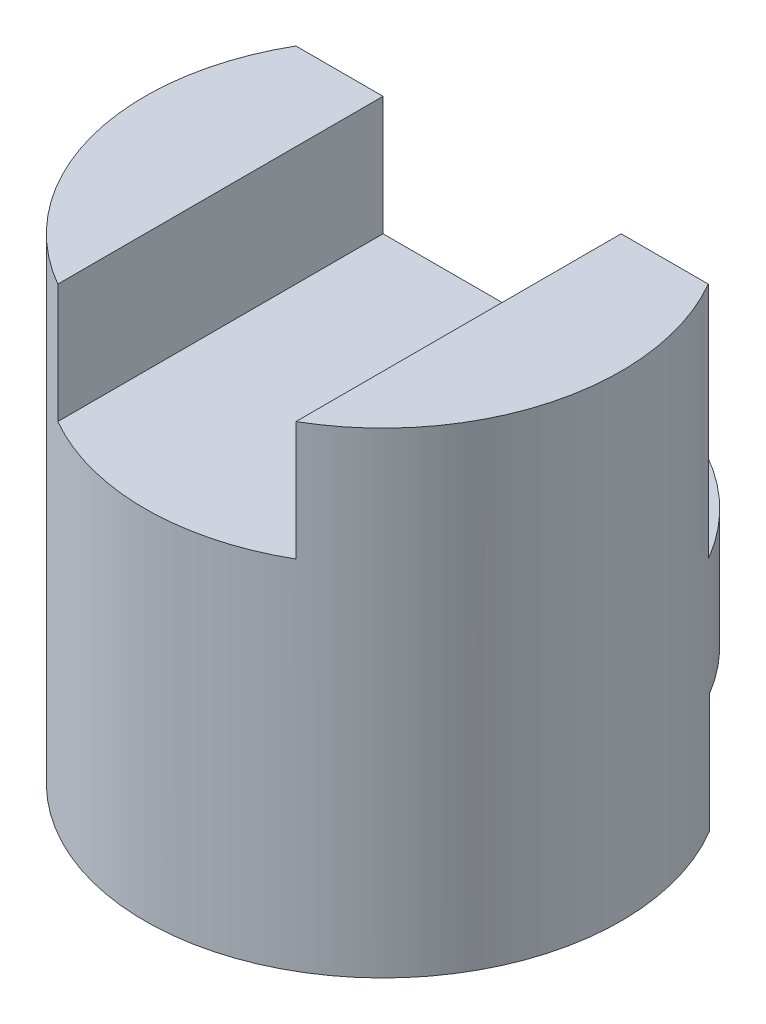
SolidWorks part; units mm, degrees
ref_plane "Front" through (0, 0, 0) normal (0, 0, 1) x (1, 0, 0)
ref_plane "Top" through (0, 0, 0) normal (0, 1, 0) x (1, 0, 0)
ref_plane "Right" through (0, 0, 0) normal (1, 0, 0) x (0, 0, -1)
sketch "Sketch1" plane through (0, 0, 0) normal (0, 1, 0) x (1, 0, 0)
  circle A0 centre (0, 0) radius 2
  dimension "D1" = 4
extrude "Boss-Extrude1" add sketch "Sketch1" along normal blind 4
sketch "Sketch2" plane through (0, 0, 0) normal (0, 0, 1) x (1, 0, 0)
  line L0 (2, 4) -> (-2, 4) construction
  line L1 (-1, 4) -> (1, 4)
  line L2 (-1, 4) -> (-1, 3)
  line L3 (-1, 3) -> (1, 3)
  line L4 (1, 4) -> (1, 3)
  line L5 (-2, 4) -> (-2, 0) construction
  dimension "D1" = 1
  dimension "D2" = 2
  dimension "D3" = 1
extrude "Cut-Extrude1" cut sketch "Sketch2" against normal mid plane 10
sketch "Sketch3" plane through (0, 4, 0) normal (0, 1, 0) x (1, 0, 0)
  line L0 (-1.7321, 1) -> (1.7321, 1)
  arc A0 (-1, 1.7321) -> (-1, -1.7321) centre (0, 0) ccw construction
  arc A1 (1, -1.7321) -> (1, 1.7321) centre (0, 0) ccw construction
  arc A2 (-1.7321, 1) -> (1.7321, 1) centre (0, 0) cw
  dimension "D1" = 1
extrude "Cut-Extrude2" cut sketch "Sketch3" against normal blind 2
sketch "Sketch4" plane through (0, 0, 0) normal (0, -1, 0) x (1, 0, 0)
  line L0 (1.7202, -1.0203) -> (-1.7202, -1.0203)
  circle A0 centre (0, 0) radius 2 construction
  arc A1 (1.7202, -1.0203) -> (-1.7202, -1.0203) centre (0, -0.0203) cw
  dimension "D1" = 1
extrude "Cut-Extrude3" cut sketch "Sketch4" against normal blind 1
